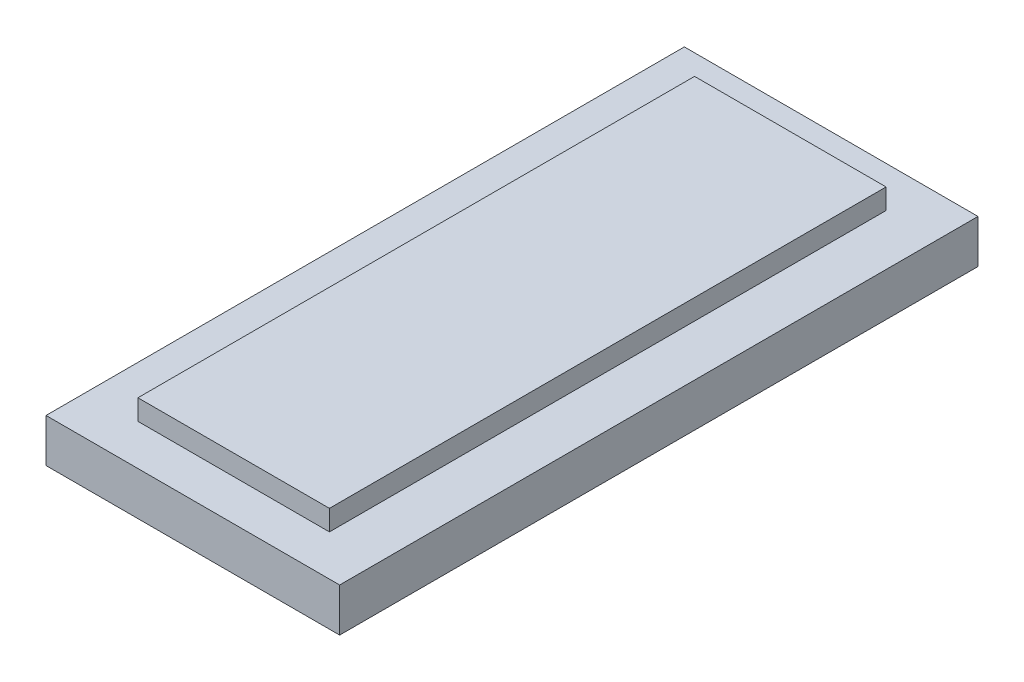
SolidWorks part; units mm, degrees
ref_plane "Front Plane" through (0, 0, 0) normal (0, 0, 1) x (1, 0, 0)
ref_plane "Top Plane" through (0, 0, 0) normal (0, 1, 0) x (1, 0, 0)
ref_plane "Right Plane" through (0, 0, 0) normal (1, 0, 0) x (0, 0, -1)
sketch "Sketch1" plane through (0, 0, 0) normal (0, 1, 0) x (1, 0, 0)
  line L1 (0, 0) -> (36.5125, 0)
  line L2 (0, 0) -> (0, 79.375)
  line L3 (0, 79.375) -> (36.5125, 79.375)
  line L4 (36.5125, 0) -> (36.5125, 79.375)
  dimension "D1" = 79.375
  dimension "D2" = 36.5125
extrude "Boss-Extrude1" add sketch "Sketch1" along normal blind 7.9375
sketch "Sketch2" plane through (0, 7.9375, 0) normal (0, 1, 0) x (1, 0, 0)
  line L0 (0, 0) -> (36.5125, 0) construction
  line L1 (36.5125, 0) -> (36.5125, 79.375) construction
  line L2 (36.5125, 79.375) -> (0, 79.375) construction
  line L3 (0, 79.375) -> (0, 0) construction
  line L4 (0, 0) -> (36.5125, 0)
  line L5 (36.5125, 0) -> (36.5125, 79.375)
  line L6 (36.5125, 79.375) -> (0, 79.375)
  line L7 (0, 79.375) -> (0, 0)
  line L8 (6.35, 74.295) -> (6.35, 5.08)
  line L9 (30.1625, 5.08) -> (30.1625, 74.295)
  line L10 (30.1625, 74.295) -> (6.35, 74.295)
  line L11 (6.35, 5.08) -> (30.1625, 5.08)
  line L12 (36.5125, 74.295) -> (0, 74.295) construction
  line L13 (6.35, 79.375) -> (6.35, 0) construction
  line L14 (30.1625, 0) -> (30.1625, 79.375) construction
  line L15 (0, 5.08) -> (36.5125, 5.08) construction
  dimension "D1" = 6.35
  dimension "D2" = 5.08
extrude "Cut-Extrude1" cut sketch "Sketch2" against normal blind 2.54
